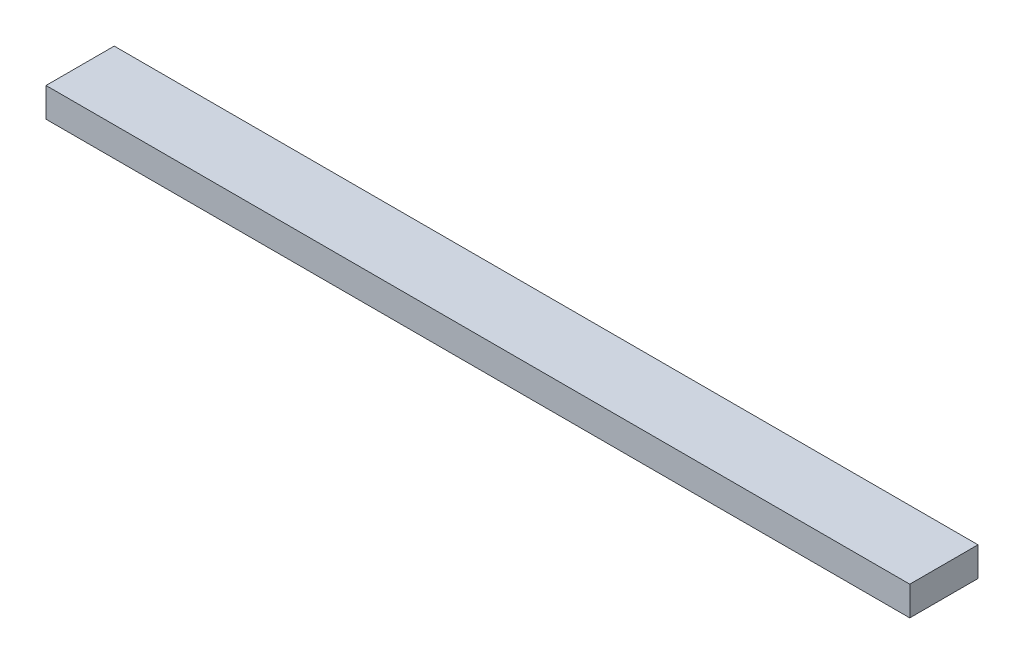
SolidWorks part; units mm, degrees
material "Pine"
ref_plane "Front Plane" through (0, 0, 0) normal (0, 0, 1) x (1, 0, 0)
ref_plane "Top Plane" through (0, 0, 0) normal (0, 1, 0) x (1, 0, 0)
ref_plane "Right Plane" through (0, 0, 0) normal (1, 0, 0) x (0, 0, -1)
sketch "Sketch1" plane through (0, 0, 0) normal (0, 1, 0) x (1, 0, 0)
  line L1 (0, 0) -> (1125.5502, 0)
  line L2 (0, 0) -> (0, 88.9)
  line L3 (0, 88.9) -> (1125.5502, 88.9)
  line L4 (1125.5502, 0) -> (1125.5502, 88.9)
  dimension "D1" = 88.9
  dimension "D2" = 1125.5502
extrude "Boss-Extrude1" add sketch "Sketch1" along normal blind 38.1
